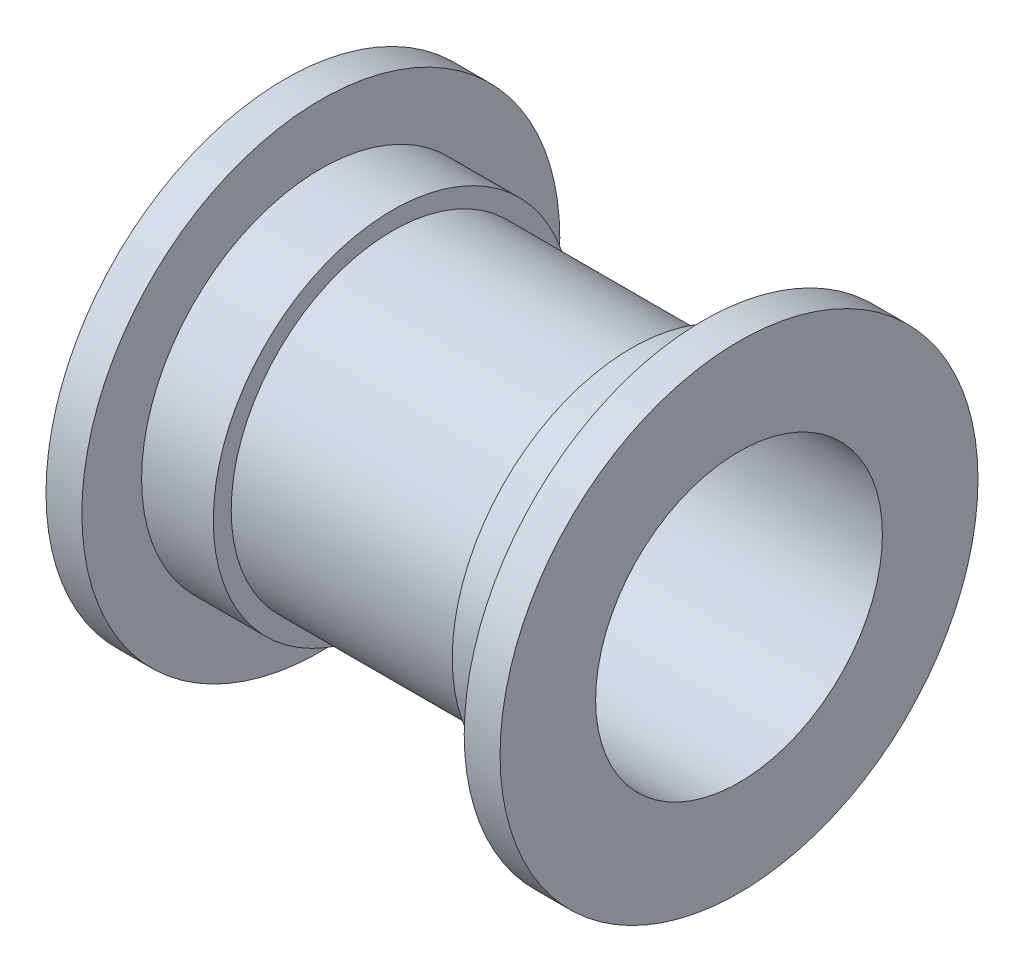
SolidWorks part; units mm, degrees
material "Brass"
ref_plane "Front Plane" through (0, 0, 0) normal (0, 0, 1) x (1, 0, 0)
ref_plane "Top Plane" through (0, 0, 0) normal (0, 1, 0) x (1, 0, 0)
ref_plane "Right Plane" through (0, 0, 0) normal (1, 0, 0) x (0, 0, -1)
sketch "Sketch3" plane through (0, 0, 0) normal (0, 0, 1) x (1, 0, 0)
  line L0 (-30.1625, 0) -> (30.1625, 0) construction
  line L1 (30.1625, 0) -> (30.1625, 31.75) construction
  line L2 (30.1625, 0) -> (30.1625, 19.05) construction
  line L3 (30.1625, 31.75) -> (30.1625, 19.05)
  line L4 (30.1625, 31.75) -> (25.4, 31.75)
  line L5 (25.4, 31.75) -> (25.4, 23.8125)
  line L6 (25.4, 23.8125) -> (15.875, 23.8125)
  line L7 (15.875, 23.8125) -> (15.875, 21.4313)
  line L8 (15.875, 21.4313) -> (-15.875, 21.4312)
  line L9 (-15.875, 21.4312) -> (-15.875, 23.8125)
  line L10 (-15.875, 23.8125) -> (-25.4, 23.8125)
  line L11 (-25.4, 23.8125) -> (-25.4, 31.75)
  line L12 (-25.4, 31.75) -> (-30.1625, 31.75)
  line L13 (-30.1625, 31.75) -> (-30.1625, 19.05)
  line L14 (-30.1625, 19.05) -> (30.1625, 19.05)
  dimension "D1" = 31.75
  dimension "D2" = 19.05
  dimension "D3" = 60.325
  dimension "D4" = 31.75
  dimension "D5" = 50.8
  dimension "D6" = 60.325
  dimension "D7" = 21.4312
  dimension "D8" = 23.8125
revolve "Revolve1" add sketch "Sketch3" angle 360 about L0
